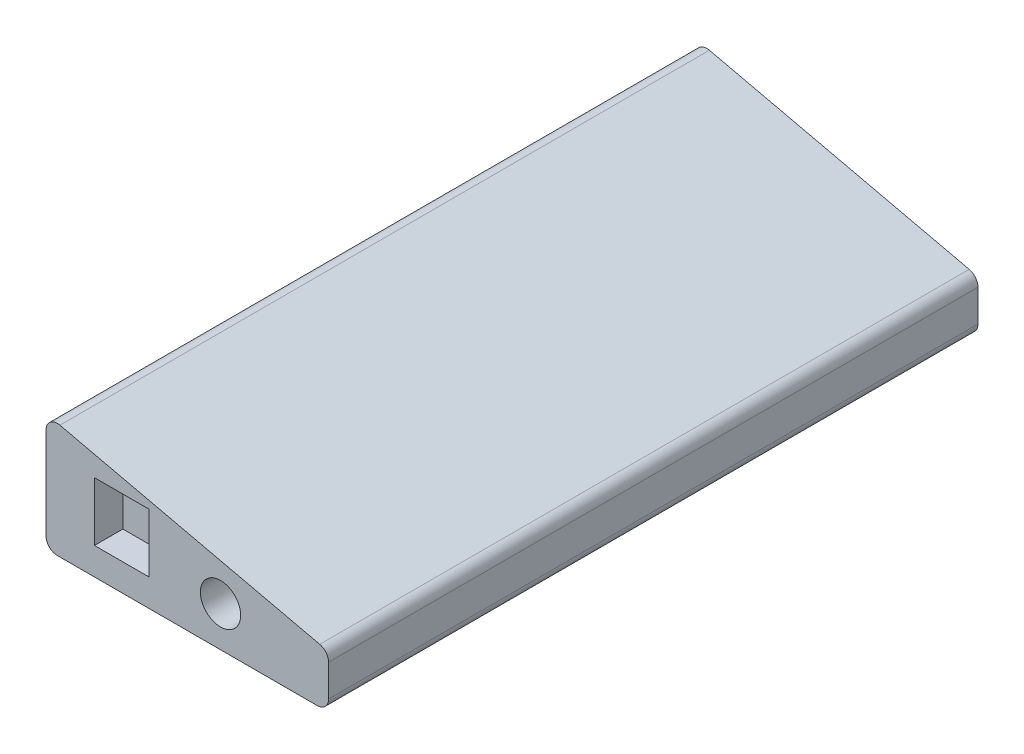
SolidWorks part; units mm, degrees
ref_plane "Front Plane" through (0, 0, 0) normal (0, 0, 1) x (1, 0, 0)
ref_plane "Top Plane" through (0, 0, 0) normal (0, 1, 0) x (1, 0, 0)
ref_plane "Right Plane" through (0, 0, 0) normal (1, 0, 0) x (0, 0, -1)
sketch "Sketch1" plane through (0, 0, 0) normal (0, 0, 1) x (1, 0, 0)
  line L0 (3.1102, 25.509) -> (61.1492, 12.1378)
  line L1 (2.54, 0) -> (60.579, 0)
  line L2 (0, 2.54) -> (0, 23.0338)
  line L4 (63.119, 2.54) -> (63.119, 9.6626)
  arc A0 (61.1492, 12.1378) -> (63.119, 9.6626) centre (60.579, 9.6626) cw
  arc A1 (60.579, 0) -> (63.119, 2.54) centre (60.579, 2.54) ccw
  arc A2 (2.54, 0) -> (0, 2.54) centre (2.54, 2.54) cw
  arc A3 (0, 23.0338) -> (3.1102, 25.509) centre (2.54, 23.0338) cw
  point P7 (63.119, 11.684)
  point P10 (63.119, 0)
  point P13 (0, 0)
  point P16 (0, 26.2255)
  dimension "D4" = 2.54
  dimension "D1" = 11.684
  dimension "D2" = 26.2255
  dimension "D3" = 63.119
extrude "Boss-Extrude1" add sketch "Sketch1" along normal blind 145.0848 contours L0 A0 L4 A1 L1 A2 L2 A3
sketch "Sketch2" plane through (0, 0, 145.0848) normal (0, 0, 1) x (1, 0, 0)
  line L1 (10.8204, 19.2151) -> (23.0124, 19.2151)
  line L2 (10.8204, 19.2151) -> (10.8204, 6.096)
  line L3 (10.8204, 6.096) -> (23.0124, 6.096)
  line L4 (23.0124, 19.2151) -> (23.0124, 6.096)
  line L5 (0, 2.54) -> (0, 23.0338) construction
  line L6 (2.54, 0) -> (60.579, 0) construction
  line L7 (63.119, 2.54) -> (63.119, 9.6626) construction
  circle A0 centre (38.989, 8.9154) radius 4.5021
  point P10 (63.119, 6.1013)
  dimension "D1" = 9.0043
  dimension "D2" = 12.192
  dimension "D3" = 13.1191
  dimension "D4" = 10.8204
  dimension "D5" = 6.096
  dimension "D6" = 24.13
  dimension "D7" = 8.9154
extrude "Cut-Extrude1" cut sketch "Sketch2" against normal blind 6.35
sketch "Sketch3" plane through (0, 0, 0) normal (-1, 0, 0) x (0, 0, 1)
  line L0 (0, 2.54) -> (0, 23.0338) construction
  line L1 (25.4, 13.1826) -> (38.5064, 13.1826)
  line L2 (25.4, 13.1826) -> (25.4, 7.1882)
  line L3 (25.4, 7.1882) -> (38.5064, 7.1882)
  line L4 (38.5064, 13.1826) -> (38.5064, 7.1882)
  line L5 (145.0848, 0) -> (0, 0) construction
  line L6 (46.482, 13.1826) -> (59.5884, 13.1826)
  line L7 (46.482, 13.1826) -> (46.482, 7.1882)
  line L8 (46.482, 7.1882) -> (59.5884, 7.1882)
  line L9 (59.5884, 13.1826) -> (59.5884, 7.1882)
  line L10 (67.564, 13.1826) -> (80.6704, 13.1826)
  line L11 (67.564, 13.1826) -> (67.564, 7.1882)
  line L12 (67.564, 7.1882) -> (80.6704, 7.1882)
  line L13 (80.6704, 13.1826) -> (80.6704, 7.1882)
  line L14 (88.646, 13.1826) -> (101.7524, 13.1826)
  line L15 (88.646, 13.1826) -> (88.646, 7.1882)
  line L16 (88.646, 7.1882) -> (101.7524, 7.1882)
  line L17 (101.7524, 13.1826) -> (101.7524, 7.1882)
  line L18 (109.728, 13.1826) -> (122.8344, 13.1826)
  line L19 (109.728, 13.1826) -> (109.728, 7.1882)
  line L20 (109.728, 7.1882) -> (122.8344, 7.1882)
  line L21 (122.8344, 13.1826) -> (122.8344, 7.1882)
  point P9 (0, 0)
  dimension "D1" = 13.1064
  dimension "D2" = 5.9944
  dimension "D3" = 25.4
  dimension "D4" = 7.1882
  dimension "D6" = 7.9756
  dimension "D5" = 5
extrude "Cut-Extrude2" cut sketch "Sketch3" against normal blind 6.35 contours L1 L4 L3 L2
sketch "Sketch4" plane through (0, 0, 0) normal (0, 0, -1) x (-1, 0, 0)
  line L0 (0, 7.1882) -> (0, 13.1826) construction
  line L1 (-7.1628, 13.1953) -> (-20.2057, 13.1953)
  line L2 (-7.1628, 13.1953) -> (-7.1628, 7.2009)
  line L3 (-7.1628, 7.2009) -> (-20.2057, 7.2009)
  line L4 (-20.2057, 13.1953) -> (-20.2057, 7.2009)
  line L5 (-2.54, 0) -> (-60.579, 0) construction
  line L6 (0, 2.54) -> (0, 23.0338) construction
  line L7 (-28.4988, 13.1953) -> (-41.5417, 13.1953)
  line L8 (-28.4988, 13.1953) -> (-28.4988, 7.2009)
  line L9 (-28.4988, 7.2009) -> (-41.5417, 7.2009)
  line L10 (-41.5417, 13.1953) -> (-41.5417, 7.2009)
  dimension "D1" = 13.0429
  dimension "D2" = 7.2009
  dimension "D3" = 7.1628
  dimension "D5" = 8.2931
  dimension "D4" = 2
extrude "Cut-Extrude3" cut sketch "Sketch4" against normal blind 6.35
